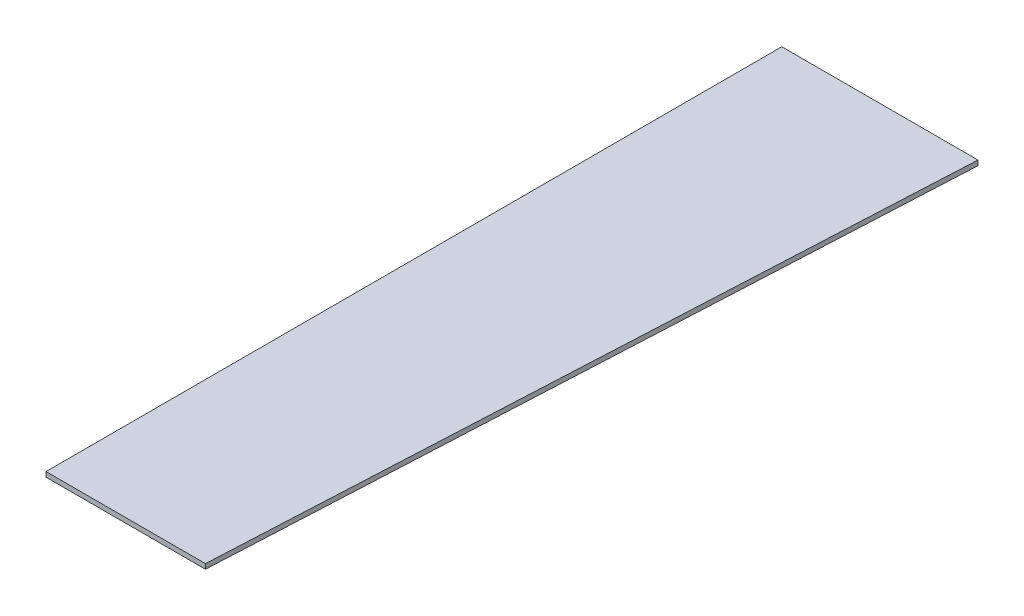
SolidWorks part; units mm, degrees
ref_plane "Face" through (0, 0, 0) normal (0, 0, 1) x (1, 0, 0)
ref_plane "Dessus" through (0, 0, 0) normal (0, 1, 0) x (1, 0, 0)
ref_plane "Droite" through (0, 0, 0) normal (1, 0, 0) x (0, 0, -1)
sketch "Esquisse1" plane through (0, 0, 0) normal (0, 1, 0) x (1, 0, 0)
  line L0 (0, 0) -> (400, 0)
  line L1 (0, 0) -> (0, -1500)
  line L2 (0, -1500) -> (325, -1500)
  line L3 (325, -1500) -> (400, 0)
  dimension "D1" = 400
  dimension "D2" = 1500
  dimension "D3" = 325
extrude "Extrusion1" add sketch "Esquisse1" along normal blind 10
